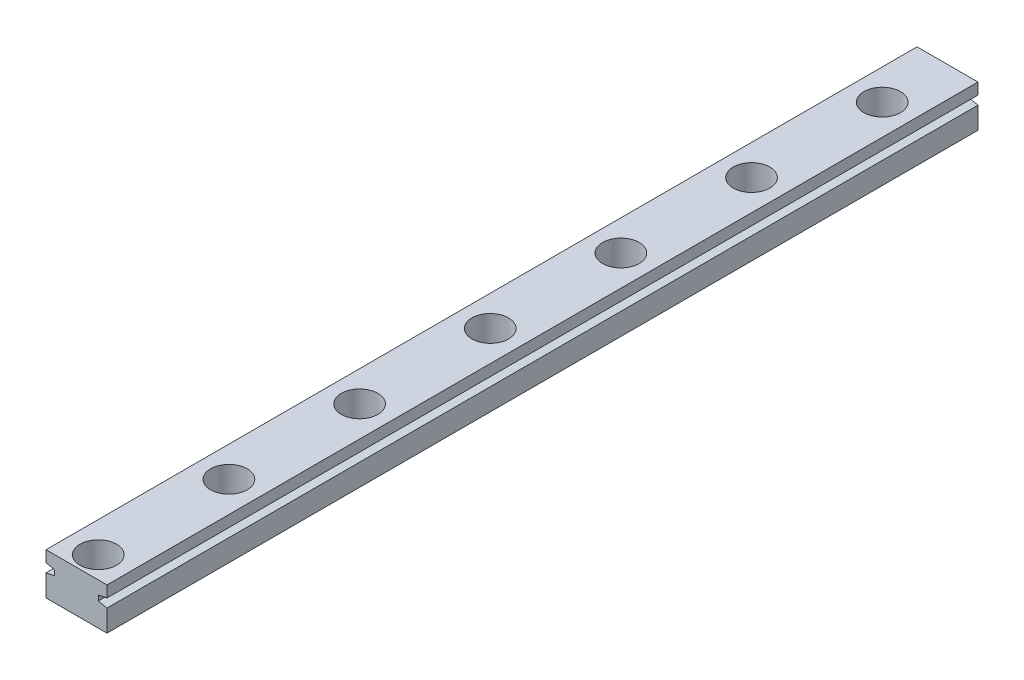
SolidWorks part; units mm, degrees
material "不锈钢 (铁素体)"
ref_plane "前视基准面" through (0, 0, 0) normal (0, 0, 1) x (1, 0, 0)
ref_plane "上视基准面" through (0, 0, 0) normal (0, 1, 0) x (1, 0, 0)
ref_plane "右视基准面" through (0, 0, 0) normal (1, 0, 0) x (0, 0, -1)
sketch "草图1" plane through (0, 0, 0) normal (0, 0, 1) x (1, 0, 0)
  line L1 (-3.5, 2.4) -> (3.5, 2.4)
  line L2 (-3.5, 2.4) -> (-3.5, -2.4)
  line L3 (-3.5, -2.4) -> (3.5, -2.4)
  line L4 (3.5, 2.4) -> (3.5, -2.4)
  line L5 (-3.5, 2.4) -> (3.5, -2.4) construction
  line L6 (-3.5, -2.4) -> (3.5, 2.4) construction
  point P0 (0, 0)
  dimension "D1" = 4.8
  dimension "D2" = 7
extrude "凸台-拉伸1" add sketch "草图1" along normal blind 100
sketch "草图2" plane through (0, 2.4, 0) normal (0, 1, 0) x (1, 0, 0)
  line L0 (0, 0) -> (0, -84.8716) construction
  line L1 (3.5, 0) -> (-3.5, 0) construction
  circle A0 centre (0, -7.5) radius 1.2
  circle A1 centre (0, -22.5) radius 1.2
  circle A2 centre (0, -37.5) radius 1.2
  circle A3 centre (0, -52.5) radius 1.2
  circle A4 centre (0, -67.5) radius 1.2
  circle A5 centre (0, -82.5) radius 1.2
  circle A6 centre (0, -97.5) radius 1.2
  circle A7 centre (0, -112.5) radius 1.2
  circle A8 centre (0, -127.5) radius 1.2
  circle A9 centre (0, -142.5) radius 1.2
  circle A10 centre (0, -157.5) radius 1.2
  circle A11 centre (0, -172.5) radius 1.2
  circle A12 centre (0, -187.5) radius 1.2
  circle A13 centre (0, -202.5) radius 1.2
  circle A14 centre (0, -217.5) radius 1.2
  circle A15 centre (0, -232.5) radius 1.2
  circle A16 centre (0, -247.5) radius 1.2
  circle A17 centre (0, -262.5) radius 1.2
  circle A18 centre (0, -277.5) radius 1.2
  circle A19 centre (0, -292.5) radius 1.2
  dimension "D1" = 2.4
  dimension "D2" = 7.5
  dimension "D4" = 15
  dimension "D3" = 20
extrude "切除-拉伸1" cut sketch "草图2" against normal through all
sketch "草图3" plane through (0, 2.4, 0) normal (0, 1, 0) x (1, 0, 0)
  circle A0 centre (0, -7.5) radius 2.1
  circle A1 centre (0, -22.5) radius 2.1
  circle A2 centre (0, -37.5) radius 2.1
  circle A3 centre (0, -52.5) radius 2.1
  circle A4 centre (0, -67.5) radius 2.1
  circle A5 centre (0, -82.5) radius 2.1
  circle A6 centre (0, -97.5) radius 2.1
  circle A7 centre (0, -112.5) radius 2.1
  circle A8 centre (0, -127.5) radius 2.1
  circle A9 centre (0, -142.5) radius 2.1
  circle A10 centre (0, -157.5) radius 2.1
  circle A11 centre (0, -172.5) radius 2.1
  circle A12 centre (0, -187.5) radius 2.1
  circle A13 centre (0, -202.5) radius 2.1
  circle A14 centre (0, -217.5) radius 2.1
  circle A15 centre (0, -232.5) radius 2.1
  circle A16 centre (0, -247.5) radius 2.1
  circle A17 centre (0, -262.5) radius 2.1
  circle A18 centre (0, -277.5) radius 2.1
  circle A19 centre (0, -292.5) radius 2.1
  dimension "D1" = 4.2
  dimension "D3" = 15
  dimension "D2" = 20
extrude "切除-拉伸2" cut sketch "草图3" against normal blind 3.5
sketch "草图4" plane through (0, 0, 0) normal (0, 0, -1) x (-1, 0, 0)
  line L0 (0, 2.4) -> (0, -2.4) construction
  line L1 (-3.5, 2.4) -> (3.5, 2.4) construction
  line L2 (3.5, -2.4) -> (-3.5, -2.4) construction
  line L3 (3.5, 1.1) -> (2.5, 0.9)
  line L4 (3.5, 2.4) -> (3.5, -2.4) construction
  line L5 (2.5, 0.9) -> (2.5, 0.3)
  line L6 (2.5, 0.3) -> (3.5, 0.1)
  line L7 (2.5, 0.6) -> (8.1318, 0.6) construction
  line L8 (3.5, 1.1) -> (3.5, 0.1)
  line L9 (-3.5, 1.1) -> (-2.5, 0.9)
  line L10 (-2.5, 0.9) -> (-2.5, 0.3)
  line L11 (-2.5, 0.3) -> (-3.5, 0.1)
  line L12 (-3.5, 1.1) -> (-3.5, 0.1)
  dimension "D1" = 1
  dimension "D2" = 1
  dimension "D3" = 0.6
  dimension "D4" = 2.3
extrude "切除-拉伸3" cut sketch "草图4" against normal through all
